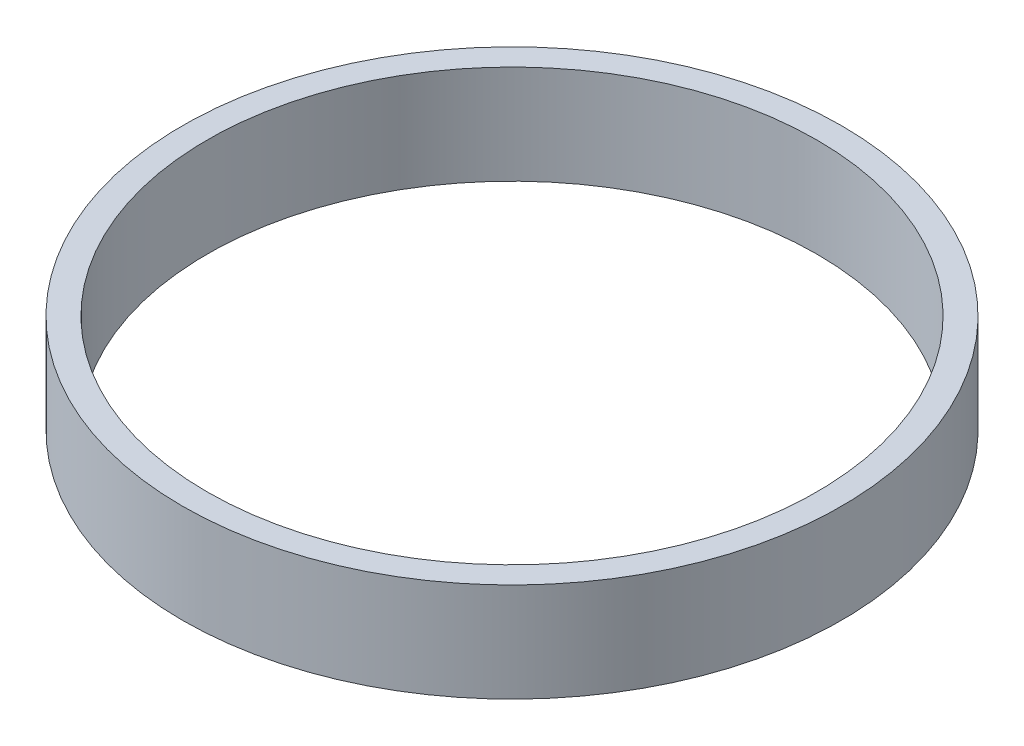
SolidWorks part; units mm, degrees
ref_plane "Front Plane" through (0, 0, 0) normal (0, 0, 1) x (1, 0, 0)
ref_plane "Top Plane" through (0, 0, 0) normal (0, 1, 0) x (1, 0, 0)
ref_plane "Right Plane" through (0, 0, 0) normal (1, 0, 0) x (0, 0, -1)
sketch "Sketch3" plane through (0, 0, 0) normal (0, 1, 0) x (1, 0, 0)
  circle A0 centre (0, 0) radius 20
extrude "Boss-Extrude1" add sketch "Sketch3" along normal blind 6
sketch "Sketch4" plane through (0, 0, 0) normal (0, 1, 0) x (1, 0, 0)
  circle A0 centre (0, 0) radius 18.5
sketch "Sketch5" plane through (0, 6, 0) normal (0, 1, 0) x (1, 0, 0)
  circle A0 centre (0, 0) radius 18.5
extrude "Cut-Extrude1" cut sketch "Sketch5" against normal blind 6
